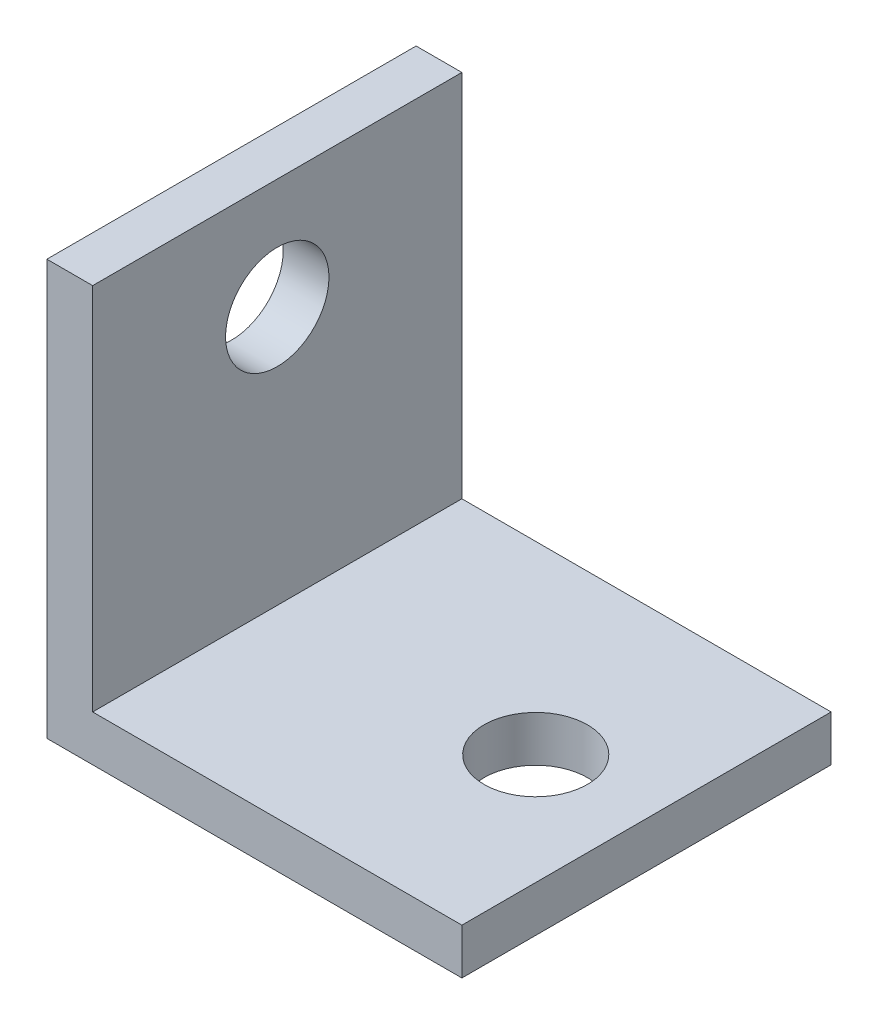
SolidWorks part; units mm, degrees
ref_plane "Front" through (0, 0, 0) normal (0, 0, 1) x (1, 0, 0)
ref_plane "Top" through (0, 0, 0) normal (0, 1, 0) x (1, 0, 0)
ref_plane "Right" through (0, 0, 0) normal (1, 0, 0) x (0, 0, -1)
sketch "Sketch1" plane through (0, 0, 0) normal (0, 0, 1) x (1, 0, 0)
  line L0 (0, 0) -> (-14.2748, 0)
  line L1 (-14.2748, 0) -> (-14.2748, 14.2748)
  line L2 (-14.2748, 14.2748) -> (-12.7, 14.2748)
  line L3 (-12.7, 14.2748) -> (-12.7, 1.5748)
  line L4 (-12.7, 1.5748) -> (0, 1.5748)
  line L5 (0, 1.5748) -> (0, 0)
  dimension "D1" = 1.5748
  dimension "D2" = 1.5748
  dimension "D3" = 14.2748
  dimension "D4" = 14.2748
extrude "Extrude1" add sketch "Sketch1" along normal blind 12.7
sketch "Sketch2" plane through (-12.7, 0, 0) normal (1, 0, 0) x (0, 0, -1)
  line L0 (-12.7, 1.5748) -> (-12.7, 14.2748) construction
  line L1 (-12.7, 0) -> (0, 0) construction
  circle A0 centre (-6.35, 10.4648) radius 1.778
  dimension "D1" = 3.556
  dimension "D2" = 6.35
  dimension "D3" = 10.4648
extrude "Cut-Extrude1" cut sketch "Sketch2" against normal blind 7.1374
sketch "Sketch4" plane through (0, 1.5748, 0) normal (0, 1, 0) x (-1, 0, 0)
  line L0 (14.2748, 6.35) -> (12.7, 6.35) construction
  line L4 (14.2748, 12.7) -> (14.2748, 0) construction
  circle A0 centre (3.81, 6.35) radius 1.778
  dimension "D1" = 3.556
  dimension "D2" = 10.4648
extrude "Cut-Extrude2" cut sketch "Sketch4" against normal blind 7.1374
